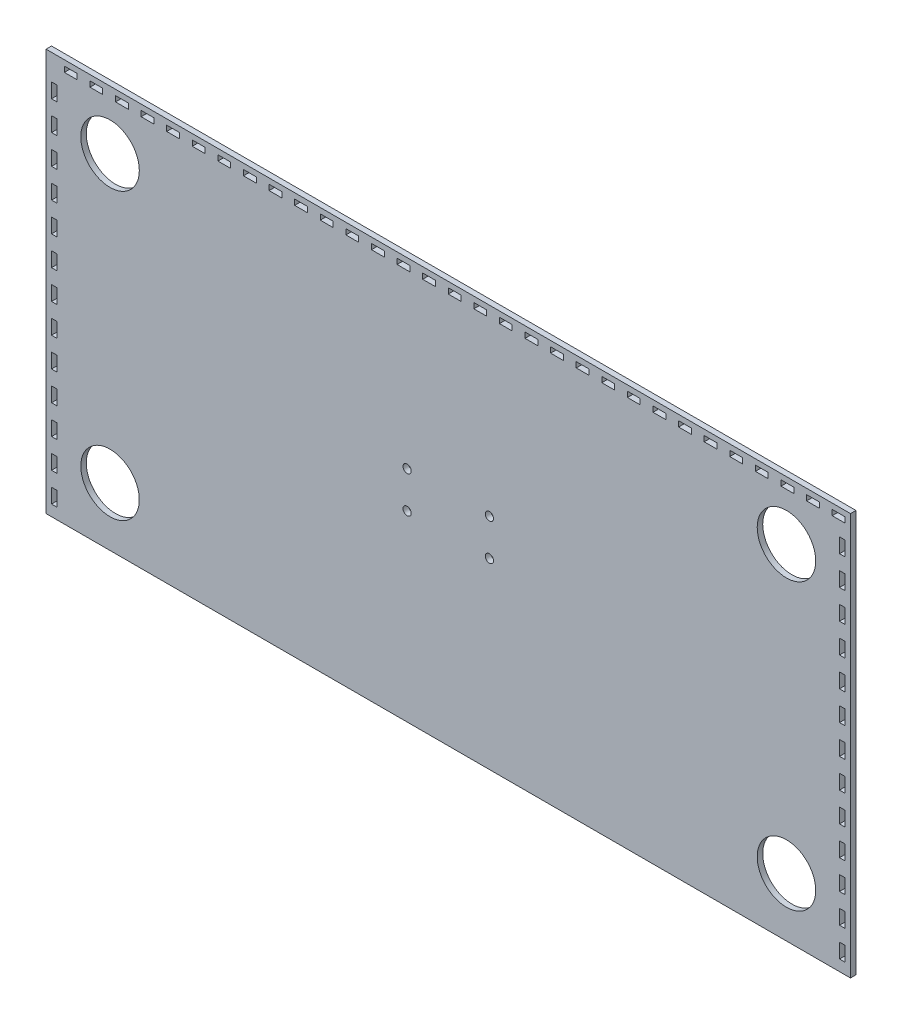
SolidWorks part; units mm, degrees
ref_plane "Plan de face" through (0, 0, 0) normal (0, 0, 1) x (1, 0, 0)
ref_plane "Plan de dessus" through (0, 0, 0) normal (0, 1, 0) x (1, 0, 0)
ref_plane "Plan de droite" through (0, 0, 0) normal (1, 0, 0) x (0, 0, -1)
sketch "Esquisse1" plane through (0, 0, 0) normal (0, 0, 1) x (1, 0, 0)
  line L1 (-220, 110) -> (220, 110)
  line L2 (-220, 110) -> (-220, -110)
  line L3 (-220, -110) -> (220, -110)
  line L4 (220, 110) -> (220, -110)
  line L5 (-220, 110) -> (220, -110) construction
  line L6 (-220, -110) -> (220, 110) construction
  point P0 (0, 0)
  dimension "D1" = 440
  dimension "D2" = 220
extrude "Boss.-Extru.1" add sketch "Esquisse1" along normal blind 3
sketch "Esquisse2" plane through (0, 0, 0) normal (0, 0, -1) x (-1, 0, 0)
  line L0 (0, 110) -> (0, -110) construction
  line L1 (-220, 110) -> (220, 110) construction
  line L2 (220, -110) -> (-220, -110) construction
  line L3 (-220, 0) -> (220, 0) construction
  line L4 (-220, -110) -> (-220, 110) construction
  line L5 (220, 110) -> (220, -110) construction
  circle A0 centre (-185, 78) radius 16
  circle A4 centre (185, 78) radius 16
  circle A5 centre (185, -78) radius 16
  circle A6 centre (-185, -78) radius 16
  dimension "D1" = 32
  dimension "D2" = 32
  dimension "D3" = 35
extrude "Enlèv. mat._Tube" cut sketch "Esquisse2" against normal blind 3
sketch "Esquisse3" plane through (0, 0, 0) normal (0, 0, -1) x (-1, 0, 0)
  line L5 (-22.5, 10) -> (22.5, 10) construction
  line L6 (-22.5, 10) -> (-22.5, -10) construction
  line L11 (-22.5, -10) -> (22.5, -10) construction
  line L12 (22.5, 10) -> (22.5, -10) construction
  line L13 (-22.5, 10) -> (22.5, -10) construction
  line L14 (-22.5, -10) -> (22.5, 10) construction
  circle A0 centre (-22.5, 10) radius 2.25
  circle A1 centre (22.5, 10) radius 2.25
  circle A2 centre (22.5, -10) radius 2.25
  circle A3 centre (-22.5, -10) radius 2.25
  point P0 (0, 0)
  dimension "D3" = 4.5
  dimension "D4" = 4.5
  dimension "D5" = 4.5
  dimension "D6" = 4.5
  dimension "D1" = 20
  dimension "D2" = 45
extrude "Enlèv. mat._Ecran" cut sketch "Esquisse3" against normal blind 3
sketch "Esquisse4" plane through (0, 0, 0) normal (0, 0, -1) x (-1, 0, 0)
  line L0 (-220, 110) -> (220, 110) construction
  line L1 (-217, 107) -> (-210, 107)
  line L2 (-217, 107) -> (-217, 104)
  line L3 (-217, 104) -> (-210, 104)
  line L4 (-210, 107) -> (-210, 104)
  line L5 (-220, -110) -> (-220, 110) construction
  line L6 (-203, 107) -> (-196, 107)
  line L7 (-203, 107) -> (-203, 104)
  line L8 (-203, 104) -> (-196, 104)
  line L9 (-196, 107) -> (-196, 104)
  line L10 (-189, 107) -> (-182, 107)
  line L11 (-189, 107) -> (-189, 104)
  line L12 (-189, 104) -> (-182, 104)
  line L13 (-182, 107) -> (-182, 104)
  line L14 (-175, 107) -> (-168, 107)
  line L15 (-175, 107) -> (-175, 104)
  line L16 (-175, 104) -> (-168, 104)
  line L17 (-168, 107) -> (-168, 104)
  line L18 (-161, 107) -> (-154, 107)
  line L19 (-161, 107) -> (-161, 104)
  line L20 (-161, 104) -> (-154, 104)
  line L21 (-154, 107) -> (-154, 104)
  line L22 (-147, 107) -> (-140, 107)
  line L23 (-147, 107) -> (-147, 104)
  line L24 (-147, 104) -> (-140, 104)
  line L25 (-140, 107) -> (-140, 104)
  line L26 (-133, 107) -> (-126, 107)
  line L27 (-133, 107) -> (-133, 104)
  line L28 (-133, 104) -> (-126, 104)
  line L29 (-126, 107) -> (-126, 104)
  line L30 (-119, 107) -> (-112, 107)
  line L31 (-119, 107) -> (-119, 104)
  line L32 (-119, 104) -> (-112, 104)
  line L33 (-112, 107) -> (-112, 104)
  line L34 (-105, 107) -> (-98, 107)
  line L35 (-105, 107) -> (-105, 104)
  line L36 (-105, 104) -> (-98, 104)
  line L37 (-98, 107) -> (-98, 104)
  line L38 (-91, 107) -> (-84, 107)
  line L39 (-91, 107) -> (-91, 104)
  line L40 (-91, 104) -> (-84, 104)
  line L41 (-84, 107) -> (-84, 104)
  line L42 (-77, 107) -> (-70, 107)
  line L43 (-77, 107) -> (-77, 104)
  line L44 (-77, 104) -> (-70, 104)
  line L45 (-70, 107) -> (-70, 104)
  line L46 (-63, 107) -> (-56, 107)
  line L47 (-63, 107) -> (-63, 104)
  line L48 (-63, 104) -> (-56, 104)
  line L49 (-56, 107) -> (-56, 104)
  line L50 (-49, 107) -> (-42, 107)
  line L51 (-49, 107) -> (-49, 104)
  line L52 (-49, 104) -> (-42, 104)
  line L53 (-42, 107) -> (-42, 104)
  line L54 (-35, 107) -> (-28, 107)
  line L55 (-35, 107) -> (-35, 104)
  line L56 (-35, 104) -> (-28, 104)
  line L57 (-28, 107) -> (-28, 104)
  line L58 (-21, 107) -> (-14, 107)
  line L59 (-21, 107) -> (-21, 104)
  line L60 (-21, 104) -> (-14, 104)
  line L61 (-14, 107) -> (-14, 104)
  line L62 (-7, 107) -> (0, 107)
  line L63 (-7, 107) -> (-7, 104)
  line L64 (-7, 104) -> (0, 104)
  line L65 (0, 107) -> (0, 104)
  line L66 (7, 107) -> (14, 107)
  line L67 (7, 107) -> (7, 104)
  line L68 (7, 104) -> (14, 104)
  line L69 (14, 107) -> (14, 104)
  line L70 (21, 107) -> (28, 107)
  line L71 (21, 107) -> (21, 104)
  line L72 (21, 104) -> (28, 104)
  line L73 (28, 107) -> (28, 104)
  line L74 (35, 107) -> (42, 107)
  line L75 (35, 107) -> (35, 104)
  line L76 (35, 104) -> (42, 104)
  line L77 (42, 107) -> (42, 104)
  line L78 (49, 107) -> (56, 107)
  line L79 (49, 107) -> (49, 104)
  line L80 (49, 104) -> (56, 104)
  line L81 (56, 107) -> (56, 104)
  line L82 (63, 107) -> (70, 107)
  line L83 (63, 107) -> (63, 104)
  line L84 (63, 104) -> (70, 104)
  line L85 (70, 107) -> (70, 104)
  line L86 (77, 107) -> (84, 107)
  line L87 (77, 107) -> (77, 104)
  line L88 (77, 104) -> (84, 104)
  line L89 (84, 107) -> (84, 104)
  line L90 (91, 107) -> (98, 107)
  line L91 (91, 107) -> (91, 104)
  line L92 (91, 104) -> (98, 104)
  line L93 (98, 107) -> (98, 104)
  line L94 (105, 107) -> (112, 107)
  line L95 (105, 107) -> (105, 104)
  line L96 (105, 104) -> (112, 104)
  line L97 (112, 107) -> (112, 104)
  line L98 (119, 107) -> (126, 107)
  line L99 (119, 107) -> (119, 104)
  line L100 (119, 104) -> (126, 104)
  line L101 (126, 107) -> (126, 104)
  line L102 (133, 107) -> (140, 107)
  line L103 (133, 107) -> (133, 104)
  line L104 (133, 104) -> (140, 104)
  line L105 (140, 107) -> (140, 104)
  line L106 (147, 107) -> (154, 107)
  line L107 (147, 107) -> (147, 104)
  line L108 (147, 104) -> (154, 104)
  line L109 (154, 107) -> (154, 104)
  line L110 (161, 107) -> (168, 107)
  line L111 (161, 107) -> (161, 104)
  line L112 (161, 104) -> (168, 104)
  line L113 (168, 107) -> (168, 104)
  line L114 (175, 107) -> (182, 107)
  line L115 (175, 107) -> (175, 104)
  line L116 (175, 104) -> (182, 104)
  line L117 (182, 107) -> (182, 104)
  line L118 (189, 107) -> (196, 107)
  line L119 (189, 107) -> (189, 104)
  line L120 (189, 104) -> (196, 104)
  line L121 (196, 107) -> (196, 104)
  line L122 (203, 107) -> (210, 107)
  line L123 (203, 107) -> (203, 104)
  line L124 (203, 104) -> (210, 104)
  line L125 (210, 107) -> (210, 104)
  dimension "D1" = 7
  dimension "D2" = 3
  dimension "D3" = 3
  dimension "D4" = 3
  dimension "D6" = 7
  dimension "D5" = 31
extrude "Enlèv. mat._CôtéArrièreBoite" cut sketch "Esquisse4" against normal blind 3
sketch "Esquisse5" plane through (0, 0, 0) normal (0, 0, -1) x (-1, 0, 0)
  line L0 (-220, -110) -> (-220, 110) construction
  line L1 (-217, -104) -> (-214, -104)
  line L2 (-217, -104) -> (-217, -96)
  line L3 (-217, -96) -> (-214, -96)
  line L4 (-214, -104) -> (-214, -96)
  line L5 (220, -110) -> (-220, -110) construction
  line L6 (0, 110) -> (0, -110) construction
  line L7 (-220, 110) -> (220, 110) construction
  line L8 (-217, -88) -> (-217, -80)
  line L9 (-217, -80) -> (-214, -80)
  line L10 (-214, -88) -> (-214, -80)
  line L11 (-217, -88) -> (-214, -88)
  line L12 (-217, -72) -> (-217, -64)
  line L13 (-217, -64) -> (-214, -64)
  line L14 (-214, -72) -> (-214, -64)
  line L15 (-217, -72) -> (-214, -72)
  line L16 (-217, -56) -> (-217, -48)
  line L17 (-217, -48) -> (-214, -48)
  line L18 (-214, -56) -> (-214, -48)
  line L19 (-217, -56) -> (-214, -56)
  line L20 (-217, -40) -> (-217, -32)
  line L21 (-217, -32) -> (-214, -32)
  line L22 (-214, -40) -> (-214, -32)
  line L23 (-217, -40) -> (-214, -40)
  line L24 (-217, -24) -> (-217, -16)
  line L25 (-217, -16) -> (-214, -16)
  line L26 (-214, -24) -> (-214, -16)
  line L27 (-217, -24) -> (-214, -24)
  line L28 (-217, -8) -> (-217, 0)
  line L29 (-217, 0) -> (-214, 0)
  line L30 (-214, -8) -> (-214, 0)
  line L31 (-217, -8) -> (-214, -8)
  line L32 (-217, 8) -> (-217, 16)
  line L33 (-217, 16) -> (-214, 16)
  line L34 (-214, 8) -> (-214, 16)
  line L35 (-217, 8) -> (-214, 8)
  line L36 (-217, 24) -> (-217, 32)
  line L37 (-217, 32) -> (-214, 32)
  line L38 (-214, 24) -> (-214, 32)
  line L39 (-217, 24) -> (-214, 24)
  line L40 (-217, 40) -> (-217, 48)
  line L41 (-217, 48) -> (-214, 48)
  line L42 (-214, 40) -> (-214, 48)
  line L43 (-217, 40) -> (-214, 40)
  line L44 (-217, 56) -> (-217, 64)
  line L45 (-217, 64) -> (-214, 64)
  line L46 (-214, 56) -> (-214, 64)
  line L47 (-217, 56) -> (-214, 56)
  line L48 (-217, 72) -> (-217, 80)
  line L49 (-217, 80) -> (-214, 80)
  line L50 (-214, 72) -> (-214, 80)
  line L51 (-217, 72) -> (-214, 72)
  line L52 (-217, 88) -> (-217, 96)
  line L53 (-217, 96) -> (-214, 96)
  line L54 (-214, 88) -> (-214, 96)
  line L55 (-217, 88) -> (-214, 88)
  line L56 (217, 88) -> (214, 88)
  line L57 (214, 88) -> (214, 96)
  line L58 (217, 96) -> (214, 96)
  line L59 (217, 88) -> (217, 96)
  line L60 (217, 72) -> (214, 72)
  line L61 (214, 72) -> (214, 80)
  line L62 (217, 80) -> (214, 80)
  line L63 (217, 72) -> (217, 80)
  line L64 (217, 56) -> (214, 56)
  line L65 (214, 56) -> (214, 64)
  line L66 (217, 64) -> (214, 64)
  line L67 (217, 56) -> (217, 64)
  line L68 (217, 40) -> (214, 40)
  line L69 (214, 40) -> (214, 48)
  line L70 (217, 48) -> (214, 48)
  line L71 (217, 40) -> (217, 48)
  line L72 (217, 24) -> (214, 24)
  line L73 (214, 24) -> (214, 32)
  line L74 (217, 32) -> (214, 32)
  line L75 (217, 24) -> (217, 32)
  line L76 (217, 8) -> (214, 8)
  line L77 (214, 8) -> (214, 16)
  line L78 (217, 16) -> (214, 16)
  line L79 (217, 8) -> (217, 16)
  line L80 (217, -8) -> (214, -8)
  line L81 (214, -8) -> (214, 0)
  line L82 (217, 0) -> (214, 0)
  line L83 (217, -8) -> (217, 0)
  line L84 (217, -24) -> (214, -24)
  line L85 (214, -24) -> (214, -16)
  line L86 (217, -16) -> (214, -16)
  line L87 (217, -24) -> (217, -16)
  line L88 (217, -40) -> (214, -40)
  line L89 (214, -40) -> (214, -32)
  line L90 (217, -32) -> (214, -32)
  line L91 (217, -40) -> (217, -32)
  line L92 (217, -56) -> (214, -56)
  line L93 (214, -56) -> (214, -48)
  line L94 (217, -48) -> (214, -48)
  line L95 (217, -56) -> (217, -48)
  line L96 (217, -72) -> (214, -72)
  line L97 (214, -72) -> (214, -64)
  line L98 (217, -64) -> (214, -64)
  line L99 (217, -72) -> (217, -64)
  line L100 (217, -88) -> (214, -88)
  line L101 (214, -88) -> (214, -80)
  line L102 (217, -80) -> (214, -80)
  line L103 (217, -88) -> (217, -80)
  line L104 (214, -104) -> (214, -96)
  line L105 (217, -96) -> (214, -96)
  line L106 (217, -104) -> (217, -96)
  line L107 (217, -104) -> (214, -104)
  dimension "D1" = 8
  dimension "D2" = 3
  dimension "D3" = 3
  dimension "D4" = 6
  dimension "D6" = 8
  dimension "D5" = 13
extrude "Enlèv. mat.-CôtéDGBoite" cut sketch "Esquisse5" against normal blind 3
